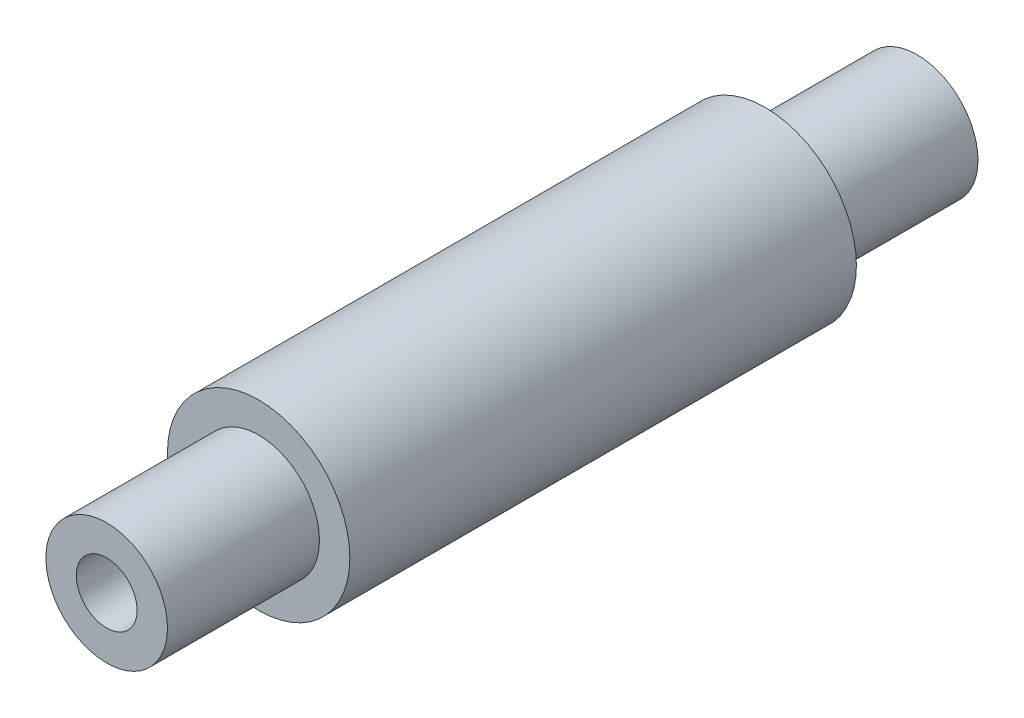
SolidWorks part; units mm, degrees
ref_plane "Front Plane" through (0, 0, 0) normal (0, 0, 1) x (1, 0, 0)
ref_plane "Top Plane" through (0, 0, 0) normal (0, 1, 0) x (1, 0, 0)
ref_plane "Right Plane" through (0, 0, 0) normal (1, 0, 0) x (0, 0, -1)
sketch "Sketch1" plane through (0, 0, 0) normal (0, 0, 1) x (1, 0, 0)
  circle A0 centre (0, 0) radius 6
  dimension "D1" = 12
extrude "Boss-Extrude1" add sketch "Sketch1" along normal mid plane 80
sketch "Sketch2" plane through (0, 0, 0) normal (0, 0, 1) x (1, 0, 0)
  circle A0 centre (0, 0) radius 9
  dimension "D1" = 18
extrude "Boss-Extrude2" add sketch "Sketch2" along normal mid plane 50
sketch "Sketch4" plane through (0, 0, 40) normal (0, 0, 1) x (1, 0, 0)
  circle A0 centre (0, 0) radius 3
  dimension "D1" = 6
extrude "Cut-Extrude1" cut sketch "Sketch4" against normal blind 45
sketch "Sketch6" plane through (0, 0, 0) normal (1, 0, 0) x (0, 0, -1)
  line L2 (-40, 6) -> (-40, -6) construction
  circle A0 centre (0, 0) radius 3
  dimension "D2" = 6
  dimension "D1" = 9
  dimension "D3" = 40
extrude "Cut-Extrude2" cut sketch "Sketch6" against normal through all
